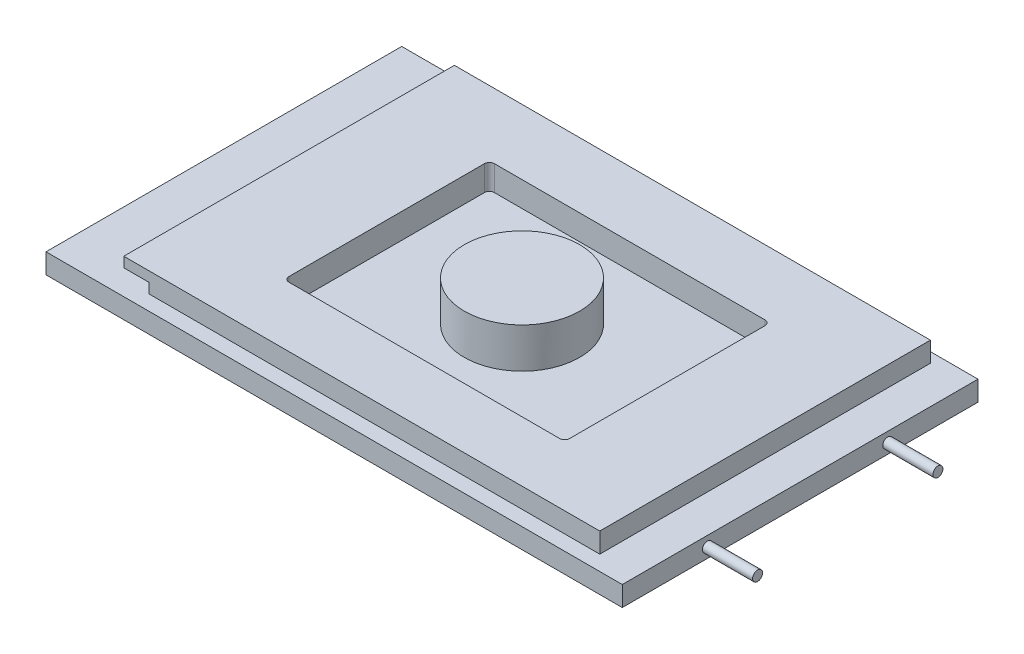
SolidWorks part; units mm, degrees
material "Beech"
ref_plane "Front Plane" through (0, 0, 0) normal (0, 0, 1) x (1, 0, 0)
ref_plane "Top Plane" through (0, 0, 0) normal (0, 1, 0) x (1, 0, 0)
ref_plane "Right Plane" through (0, 0, 0) normal (1, 0, 0) x (0, 0, -1)
other "Configuration Table"
sketch "Sketch1" plane through (0, 0, 0) normal (0, 1, 0) x (1, 0, 0)
  line L1 (0, 0) -> (115.0112, 0)
  line L2 (0, 0) -> (0, 70.993)
  line L3 (0, 70.993) -> (115.0112, 70.993)
  line L4 (115.0112, 0) -> (115.0112, 70.993)
  dimension "D1" = 115.0112
  dimension "D2" = 70.993
extrude "Boss-Extrude1" add sketch "Sketch1" along normal blind 3.9878
sketch "Sketch2" plane through (0, 3.9878, 0) normal (0, 1, 0) x (1, 0, 0)
  line L1 (17.526, 68.9864) -> (107.5182, 68.9864)
  line L2 (17.526, 68.9864) -> (17.526, 2.9972)
  line L3 (17.526, 2.9972) -> (107.5182, 2.9972)
  line L4 (107.5182, 68.9864) -> (107.5182, 2.9972)
  line L5 (0, 0) -> (115.0112, 0) construction
  line L6 (115.0112, 0) -> (115.0112, 70.993) construction
  dimension "D1" = 89.9922
  dimension "D2" = 7.493
  dimension "D3" = 2.9972
  dimension "D4" = 65.9892
extrude "Boss-Extrude2" add sketch "Sketch2" along normal blind 1.999
sketch "Sketch3" plane through (0, 0, -2.9972) normal (0, 0, 1) x (1, 0, 0)
  line L0 (17.526, 5.9868) -> (12.5222, 5.9868)
  line L1 (12.5222, 5.9868) -> (12.5222, 7.9858)
  line L2 (12.5222, 7.9858) -> (107.5182, 7.9858)
  line L3 (107.5182, 7.9858) -> (107.5182, 5.9868)
  line L4 (17.526, 5.9868) -> (107.5182, 5.9868) construction
  line L5 (17.526, 5.9868) -> (107.5182, 5.9868)
  dimension "D1" = 5.0038
  dimension "D2" = 1.999
extrude "Boss-Extrude3" add sketch "Sketch3" against normal blind 65.9892
sketch "Sketch4" plane through (0, 7.9858, 0) normal (0, 1, 0) x (1, 0, 0)
  line L0 (12.5222, 68.9864) -> (12.5222, 2.9972) construction
  line L1 (33.5026, 14.986) -> (87.5284, 14.986)
  line L2 (32.512, 15.9766) -> (32.512, 54.991)
  line L3 (33.5026, 55.9816) -> (87.5284, 55.9816)
  line L4 (88.519, 15.9766) -> (88.519, 54.991)
  line L5 (107.5182, 2.9972) -> (12.5222, 2.9972) construction
  arc A0 (87.5284, 55.9816) -> (88.519, 54.991) centre (87.5284, 54.991) cw
  arc A1 (88.519, 15.9766) -> (87.5284, 14.986) centre (87.5284, 15.9766) cw
  arc A2 (33.5026, 14.986) -> (32.512, 15.9766) centre (33.5026, 15.9766) cw
  arc A3 (32.512, 54.991) -> (33.5026, 55.9816) centre (33.5026, 54.991) cw
  point P10 (88.519, 55.9816)
  point P13 (88.519, 14.986)
  point P18 (32.512, 55.9816)
  dimension "D5" = 0.9906
  dimension "D1" = 40.9956
  dimension "D2" = 56.007
  dimension "D3" = 19.9898
  dimension "D4" = 11.9888
extrude "Cut-Extrude1" cut sketch "Sketch4" against normal blind 5.0038
sketch "Sketch5" plane through (0, 2.982, 0) normal (0, 1, 0) x (1, 0, 0)
  line L0 (0, 0) -> (115.0112, 0) construction
  line L1 (0, 70.993) -> (0, 0) construction
  circle A0 centre (59.0042, 35.9918) radius 11.5062
  dimension "D1" = 23.0124
  dimension "D2" = 35.9918
  dimension "D3" = 59.0042
extrude "Boss-Extrude4" add sketch "Sketch5" along normal blind 8.001
sketch "Sketch6" plane through (115.0112, 0, 0) normal (1, 0, 0) x (0, 0, -1)
  line L0 (0, 0) -> (70.993, 0) construction
  line L1 (70.993, 3.9878) -> (70.993, 0) construction
  line L2 (0, 3.9878) -> (0, 0) construction
  circle A0 centre (16.9926, 1.999) radius 0.9995
  circle A1 centre (52.9844, 1.999) radius 0.9995
  point P8 (0, 0)
  point P9 (0, 0)
  dimension "D1" = 1.999
  dimension "D2" = 18.0086
  dimension "D3" = 1.999
  dimension "D4" = 16.9926
extrude "Boss-Extrude5" add sketch "Sketch6" along normal blind 10.0076
